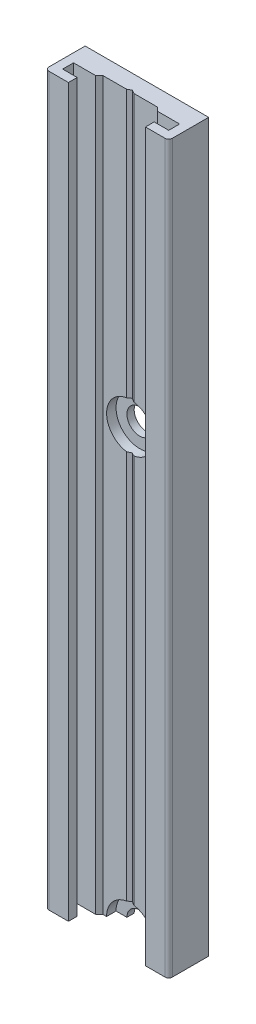
SolidWorks part; units mm, degrees
ref_plane "Front Plane" through (0, 0, 0) normal (0, 0, 1) x (1, 0, 0)
ref_plane "Top Plane" through (0, 0, 0) normal (0, 1, 0) x (1, 0, 0)
ref_plane "Right Plane" through (0, 0, 0) normal (1, 0, 0) x (0, 0, -1)
ref_plane "Plane1" through (0, 100, 0) normal (0, 1, 0) x (1, 0, 0)
sketch "Sketch1" plane through (0, 100, 0) normal (0, 1, 0) x (1, 0, 0)
  line L0 (-8, -5.5) -> (8, -5.5)
  line L1 (8.5, -5) -> (8.5, 0)
  line L2 (8.5, 0) -> (-8.5, 0)
  line L3 (-8.5, 0) -> (-8.5, -5)
  arc A0 (-8.5, -5) -> (-8, -5.5) centre (-8, -5) ccw
  arc A1 (8, -5.5) -> (8.5, -5) centre (8, -5) ccw
extrude "Boss-Extrude1" add sketch "Sketch1" against normal blind 100
sketch "Sketch2" plane through (0, 0, 0) normal (0, -1, 0) x (1, 0, 0)
  line L0 (5.3, 5.5) -> (-5.3, 5.5)
  line L1 (-5.3, 5.5) -> (-5.3, 4.3)
  line L2 (-5.3, 4.3) -> (-7.3, 4.3)
  line L3 (-7.3, 4.3) -> (-7.3, 2.8)
  line L4 (-7.3, 2.8) -> (-3.75, 2.8)
  line L5 (-3.75, 2.8) -> (-3.75, 2.3)
  line L6 (-3.75, 2.3) -> (-0.5, 2.3)
  line L7 (-0.5, 2.3) -> (0.5, 1.7226)
  line L8 (0.5, 1.7226) -> (0.5, 2.3)
  line L9 (0.5, 2.3) -> (3.75, 2.3)
  line L10 (3.75, 2.3) -> (3.75, 2.8)
  line L11 (3.75, 2.8) -> (7.3, 2.8)
  line L12 (7.3, 2.8) -> (7.3, 4.3)
  line L13 (7.3, 4.3) -> (5.3, 4.3)
  line L14 (5.3, 4.3) -> (5.3, 5.5)
extrude "Cut-Extrude1" cut sketch "Sketch2" against normal through all
draft "Draft1" type of draft neutral plane draft angle 45 faces to draft 1 face at (-3.75, 50, 2.55) neutral plane through (-3.75, 100, 2.3) neutral plane normal (0, 0, 1) parameters "D1"=45
draft "Draft2" type of draft neutral plane draft angle 45 faces to draft 1 face at (3.75, 50, 2.55) neutral plane through (0.5, 100, 2.3) neutral plane normal (0, 0, 1) parameters "D1"=45
draft "Draft3" type of draft neutral plane draft angle 60 faces to draft 1 face at (0.5, 50, 2.0113) neutral plane through (0.5, 100, 2.3) neutral plane normal (0, 0, 1) parameters "D1"=60
ref_plane "Plane2" through (0, -60, 0) normal (0, 1, 0) x (1, 0, 0)
sketch "Sketch3" plane through (0, -60, 0) normal (0, 1, 0) x (1, 0, 0)
  line L0 (1.75, 0) -> (0, 0)
  line L1 (0, 0) -> (0, -2.3)
  line L2 (0, -2.3) -> (3.25, -2.3)
  line L3 (3.25, -2.3) -> (3.25, -1)
  line L4 (3.25, -1) -> (1.75, -1)
  line L5 (1.75, -1) -> (1.75, 0)
  line L6 (0, 0) -> (0, -2.3) construction
revolve "Cut-Revolve1" [suppressed] cut sketch "Sketch3" angle 360 about L6
sketch "Sketch4" plane through (0, 0, 0) normal (0, 1, 0) x (1, 0, 0)
  line L0 (1.75, 0) -> (0, 0)
  line L1 (0, 0) -> (0, -2.3)
  line L2 (0, -2.3) -> (3.25, -2.3)
  line L3 (3.25, -2.3) -> (3.25, -1)
  line L4 (3.25, -1) -> (1.75, -1)
  line L5 (1.75, -1) -> (1.75, 0)
  line L6 (0, 0) -> (0, -2.3) construction
revolve "Cut-Revolve2" cut sketch "Sketch4" angle 360 about L6
ref_plane "Plane3" through (0, 60, 0) normal (0, 1, 0) x (1, 0, 0)
sketch "Sketch5" plane through (0, 60, 0) normal (0, 1, 0) x (1, 0, 0)
  line L0 (1.75, 0) -> (0, 0)
  line L1 (0, 0) -> (0, -2.3)
  line L2 (0, -2.3) -> (3.25, -2.3)
  line L3 (3.25, -2.3) -> (3.25, -1)
  line L4 (3.25, -1) -> (1.75, -1)
  line L5 (1.75, -1) -> (1.75, 0)
  line L6 (0, 0) -> (0, -2.3) construction
revolve "Cut-Revolve3" cut sketch "Sketch5" angle 360 about L6
